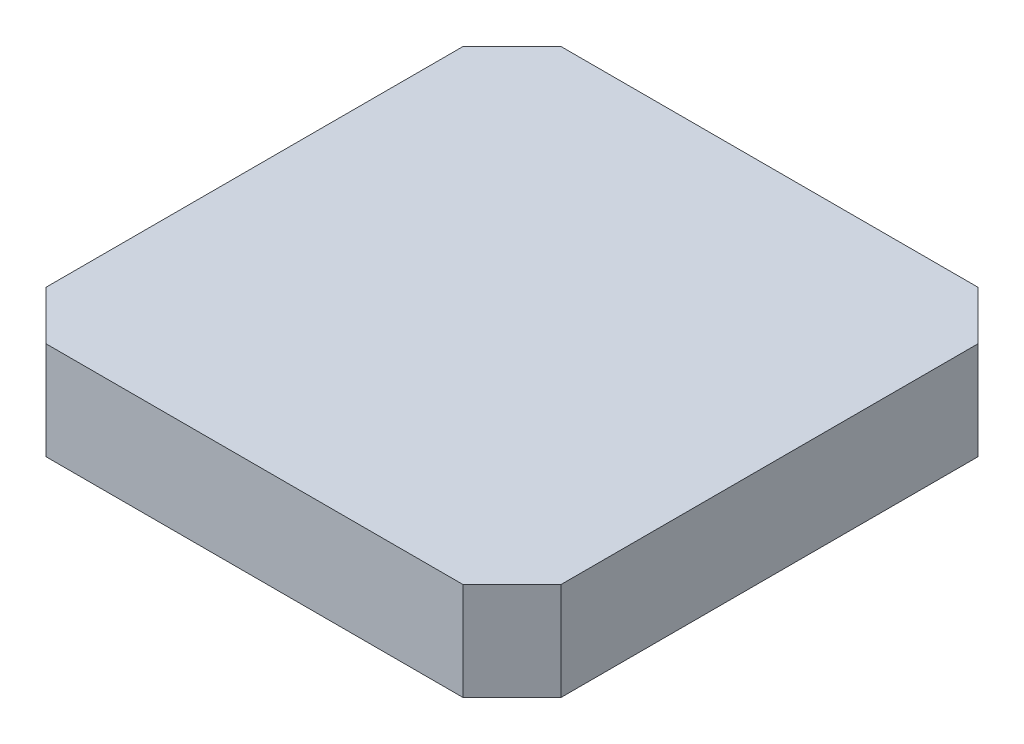
SolidWorks part; units mm, degrees
ref_plane "Front" through (0, 0, 0) normal (0, 0, 1) x (1, 0, 0)
ref_plane "Top" through (0, 0, 0) normal (0, 1, 0) x (1, 0, 0)
ref_plane "Right" through (0, 0, 0) normal (1, 0, 0) x (0, 0, -1)
sketch "Sketch2" plane through (0, 0, 0) normal (0, 1, 0) x (1, 0, 0)
  line L6 (-21.05, -21.05) -> (21.05, -21.05)
  line L10 (-21.05, -21.05) -> (-21.05, 21.05)
  line L11 (-21.05, 21.05) -> (21.05, 21.05)
  line L12 (21.05, -21.05) -> (21.05, 21.05)
  line L13 (-21.05, -21.05) -> (21.05, 21.05) construction
  line L14 (-21.05, 21.05) -> (21.05, -21.05) construction
  point P0 (0, 0)
  dimension "D1" = 42.1
extrude "Boss-Extrude1" add sketch "Sketch2" along normal blind 8
chamfer "Chamfer3" distance 4 angle 45 4 edges at (21.05, 4, -21.05) (21.05, 4, 21.05) (-21.05, 4, -21.05) (-21.05, 4, 21.05)
